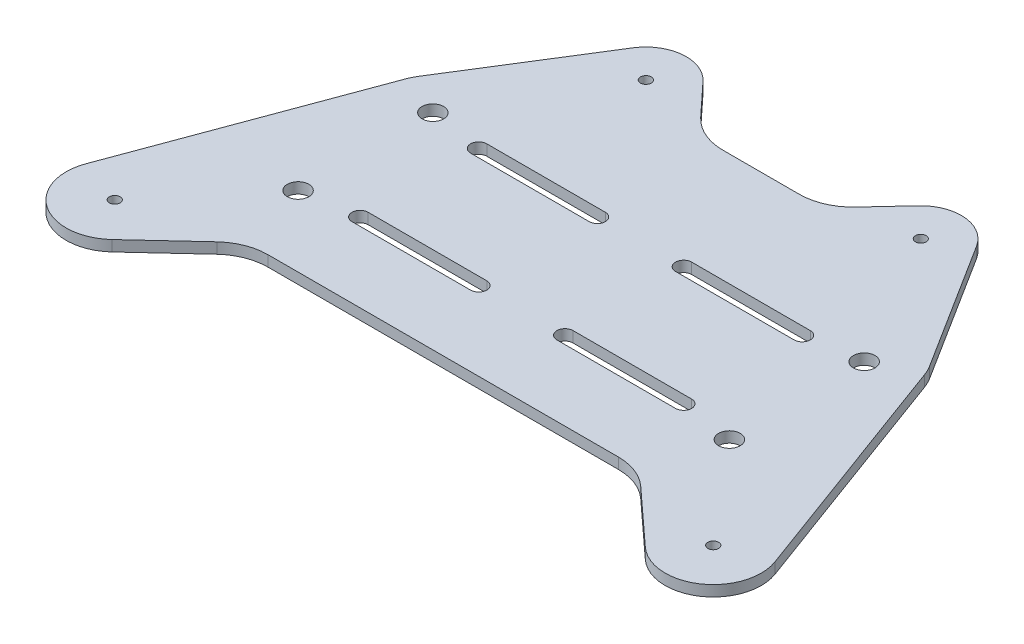
SolidWorks part; units mm, degrees
ref_plane "Front Plane" through (0, 0, 0) normal (0, 0, 1) x (1, 0, 0)
ref_plane "Top Plane" through (0, 0, 0) normal (0, 1, 0) x (1, 0, 0)
ref_plane "Right Plane" through (0, 0, 0) normal (1, 0, 0) x (0, 0, -1)
sketch "Sketch1" plane through (0, 0, 0) normal (0, 1, 0) x (1, 0, 0)
  line L1 (-8.2126, -4.5965) -> (121.7874, -4.5965)
  line L2 (-8.2126, -4.5965) -> (-8.2126, 85.4035)
  line L3 (-8.2126, 85.4035) -> (121.7874, 85.4035)
  line L4 (121.7874, -4.5965) -> (121.7874, 85.4035)
  dimension "D1" = 130
  dimension "D2" = 90
extrude "Boss-Extrude2" add sketch "Sketch1" along normal blind 2
sketch "Sketch2" plane through (0, 2, 0) normal (0, 1, 0) x (1, 0, 0)
  line L0 (121.7874, 85.4035) -> (-8.2126, 85.4035) construction
  line L1 (16.7874, 52.9035) -> (96.7874, 52.9035)
  line L2 (16.7874, 52.9035) -> (16.7874, 27.9035)
  line L3 (16.7874, 27.9035) -> (96.7874, 27.9035)
  line L4 (96.7874, 52.9035) -> (96.7874, 27.9035)
  line L5 (-8.2126, 85.4035) -> (-8.2126, -4.5965) construction
  circle A0 centre (16.7874, 52.9035) radius 2
  circle A1 centre (16.7874, 27.9035) radius 2
  circle A2 centre (96.7874, 52.9035) radius 2
  circle A3 centre (96.7874, 27.9035) radius 2
  point P6 (16.7874, 40.4035)
  point P7 (56.7874, 52.9035)
  dimension "D1" = 25
  dimension "D2" = 80
  dimension "D3" = 45
  dimension "D4" = 65
extrude "Cut-Extrude1" cut sketch "Sketch2" against normal blind 10 contours A0 | A1 | A3 | A2
sketch "Sketch4" plane through (0, 2, 0) normal (0, 1, 0) x (1, 0, 0)
  line L0 (26.7874, 51.4035) -> (48.7874, 51.4035) construction
  line L1 (26.7874, 52.9035) -> (48.7874, 52.9035)
  line L2 (26.7874, 49.9035) -> (48.7874, 49.9035)
  line L3 (26.7874, 29.4035) -> (48.7874, 29.4035) construction
  line L4 (26.7874, 30.9035) -> (48.7874, 30.9035)
  line L5 (26.7874, 27.9035) -> (48.7874, 27.9035)
  line L6 (64.7874, 51.4035) -> (86.7874, 51.4035) construction
  line L7 (64.7874, 52.9035) -> (86.7874, 52.9035)
  line L8 (64.7874, 49.9035) -> (86.7874, 49.9035)
  line L9 (64.7874, 29.4035) -> (86.7874, 29.4035) construction
  line L10 (64.7874, 30.9035) -> (86.7874, 30.9035)
  line L11 (64.7874, 27.9035) -> (86.7874, 27.9035)
  arc A0 (26.7874, 52.9035) -> (26.7874, 49.9035) centre (26.7874, 51.4035) ccw
  arc A1 (48.7874, 49.9035) -> (48.7874, 52.9035) centre (48.7874, 51.4035) ccw
  arc A2 (26.7874, 30.9035) -> (26.7874, 27.9035) centre (26.7874, 29.4035) ccw
  arc A3 (48.7874, 27.9035) -> (48.7874, 30.9035) centre (48.7874, 29.4035) ccw
  arc A4 (64.7874, 52.9035) -> (64.7874, 49.9035) centre (64.7874, 51.4035) ccw
  arc A5 (86.7874, 49.9035) -> (86.7874, 52.9035) centre (86.7874, 51.4035) ccw
  arc A6 (64.7874, 30.9035) -> (64.7874, 27.9035) centre (64.7874, 29.4035) ccw
  arc A7 (86.7874, 27.9035) -> (86.7874, 30.9035) centre (86.7874, 29.4035) ccw
  circle A8 centre (16.7874, 27.9035) radius 2 construction
  circle A10 centre (16.7874, 52.9035) radius 2 construction
  circle A12 centre (96.7874, 27.9035) radius 2 construction
  circle A14 centre (96.7874, 52.9035) radius 2 construction
  point P2 (37.7874, 51.4035)
  point P7 (37.7874, 29.4035)
  point P14 (75.7874, 51.4035)
  point P21 (75.7874, 29.4035)
  dimension "D1" = 1.5
  dimension "D2" = 1.5
  dimension "D3" = 1.5
  dimension "D5" = 1.5
  dimension "D4" = 10
  dimension "D13" = 10
  dimension "D14" = 10
  dimension "D6" = 22
  dimension "D7" = 22
  dimension "D8" = 22
  dimension "D9" = 22
  dimension "D10" = 22
  dimension "D11" = 23.5
  dimension "D12" = 0
extrude "Cut-Extrude3" cut sketch "Sketch4" against normal blind 10
sketch "Sketch5" plane through (0, 2, 0) normal (0, 1, 0) x (1, 0, 0)
  line L0 (-8.2126, 40.4035) -> (121.7874, 40.4035) construction
  line L1 (-8.2126, 85.4035) -> (-8.2126, -4.5965) construction
  line L2 (121.7874, -4.5965) -> (121.7874, 85.4035) construction
  line L3 (56.7874, 85.4035) -> (56.7874, -4.5965) construction
  line L4 (121.7874, 85.4035) -> (-8.2126, 85.4035) construction
  line L5 (-8.2126, -4.5965) -> (121.7874, -4.5965) construction
  circle A0 centre (1.2874, 9.4035) radius 1
  circle A1 centre (112.2874, 9.4035) radius 1
  circle A2 centre (31.2874, 77.9035) radius 1
  circle A3 centre (82.2874, 77.9035) radius 1
  dimension "D1" = 111
  dimension "D2" = 55.5
  dimension "D3" = 31
  dimension "D4" = 2
  dimension "D5" = 2
  dimension "D6" = 68.5
  dimension "D8" = 51
  dimension "D9" = 25.5
  dimension "D7" = 0
extrude "Cut-Extrude4" cut sketch "Sketch5" against normal blind 10
sketch "Sketch6" plane through (0, 2, 0) normal (0, 1, 0) x (1, 0, 0)
  line L0 (19.7874, 85.4035) -> (-8.3349, 9.4035)
  line L1 (121.7874, 85.4035) -> (-8.2126, 85.4035) construction
  line L2 (68.2134, 73.7782) -> (76.794, 83.0096)
  line L3 (24.929, 81.8809) -> (9.6108, 57.3927)
  line L4 (93.7874, 85.4035) -> (121.7874, 9.4035)
  line L5 (121.7874, -4.5965) -> (121.7874, 85.4035) construction
  line L6 (7.4251, 2.7878) -> (20.3789, 14.8057)
  line L7 (20.3789, 14.8057) -> (93.196, 14.8057)
  line L8 (93.196, 14.8057) -> (106.2653, 2.8309)
  line L9 (36.7808, 83.0096) -> (45.3615, 73.7782)
  line L10 (45.3615, 73.7782) -> (68.2134, 73.7782)
  line L11 (104.1072, 57.3927) -> (88.6292, 81.9075)
  circle A0 centre (112.2874, 9.4035) radius 1 construction
  circle A1 centre (1.2874, 9.4035) radius 1 construction
  circle A2 centre (1.2874, 9.4035) radius 9.0243
  circle A3 centre (112.2874, 9.4035) radius 8.9143
  circle A4 centre (31.2874, 77.9035) radius 7.5
  circle A5 centre (16.7874, 52.9035) radius 8.465
  circle A6 centre (96.7874, 52.9035) radius 8.4204
  circle A7 centre (82.2874, 77.9035) radius 7.5
  circle A8 centre (31.2874, 77.9035) radius 1 construction
  circle A9 centre (82.2874, 77.9035) radius 1 construction
  dimension "D5" = 19.0914
  dimension "D1" = 28
  dimension "D2" = 0
  dimension "D3" = 28
  dimension "D4" = 19.0914
  dimension "D6" = 14.0741
  dimension "D7" = 14.0741
extrude "Cut-Extrude5" cut sketch "Sketch6" against normal through all
fillet "Fillet1" radius 10 5 edges at (45.3615, 1, -73.7782) (68.2134, 1, -73.7782) (93.196, 1, -14.8057) (20.3789, 1, -14.8057) (104.1072, 1, -57.3927)
